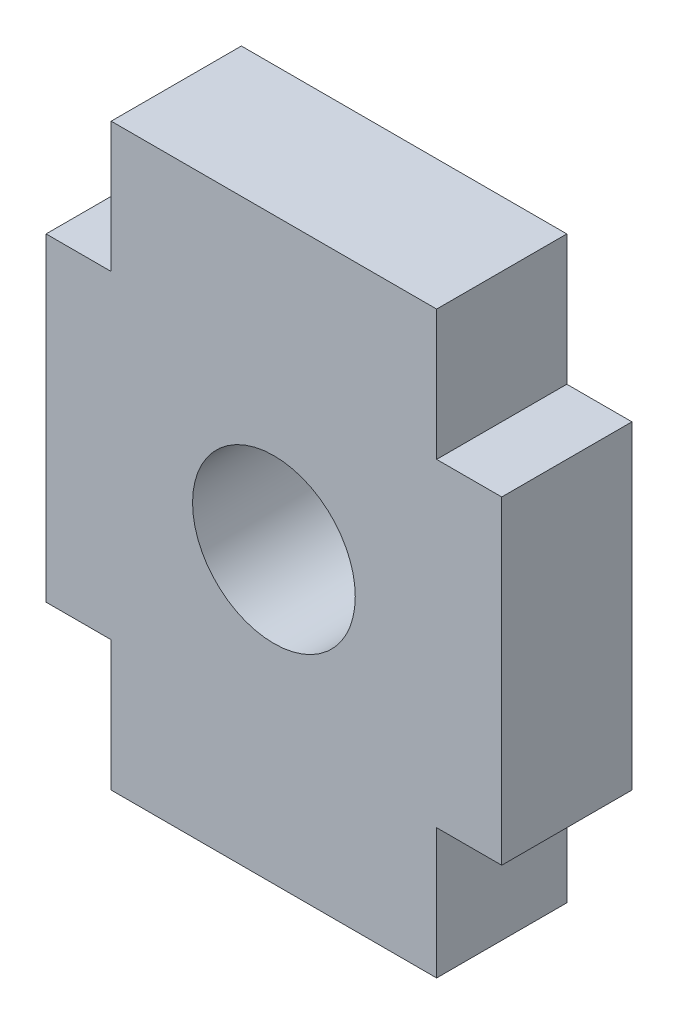
SolidWorks part; units mm, degrees
ref_plane "Front Plane" through (0, 0, 0) normal (0, 0, 1) x (1, 0, 0)
ref_plane "Top Plane" through (0, 0, 0) normal (0, 1, 0) x (1, 0, 0)
ref_plane "Right Plane" through (0, 0, 0) normal (1, 0, 0) x (0, 0, -1)
sketch "Sketch1" plane through (0, 0, 0) normal (0, 0, 1) x (1, 0, 0)
  line L0 (1952.1768, 1465.7841) -> (1957.1768, 1465.7841)
  line L1 (1952.1768, 1456.8841) -> (1957.1768, 1456.8841)
  line L3 (1957.1768, 1458.8841) -> (1957.1768, 1456.8841)
  line L4 (1957.1768, 1458.8841) -> (1958.1768, 1458.8841)
  line L5 (1958.1768, 1463.7841) -> (1958.1768, 1458.8841)
  line L6 (1957.1768, 1463.7841) -> (1957.1768, 1465.7841)
  line L7 (1957.1768, 1463.7841) -> (1958.1768, 1463.7841)
  line L37 (1952.1768, 1458.8841) -> (1951.1768, 1458.8841)
  line L40 (1952.1768, 1458.8841) -> (1952.1768, 1456.8841)
  line L127 (1952.1768, 1463.7841) -> (1951.1768, 1463.7841)
  line L130 (1952.1768, 1463.7841) -> (1952.1768, 1465.7841)
  line L131 (1951.1768, 1463.7841) -> (1951.1768, 1458.8841)
  circle A82 centre (1954.6768, 1461.3341) radius 1.25
  dimension "D5" = 1957.1768
  dimension "D1" = 2.5
  dimension "D2" = 1951.1768
  dimension "D3" = 1952.1768
  dimension "D4" = 1954.6768
  dimension "D6" = 1456.8841
  dimension "D7" = 1458.8841
  dimension "D8" = 1461.3341
  dimension "D9" = 1463.7841
extrude "Boss-Extrude1" add sketch "Sketch1" along normal blind 2
